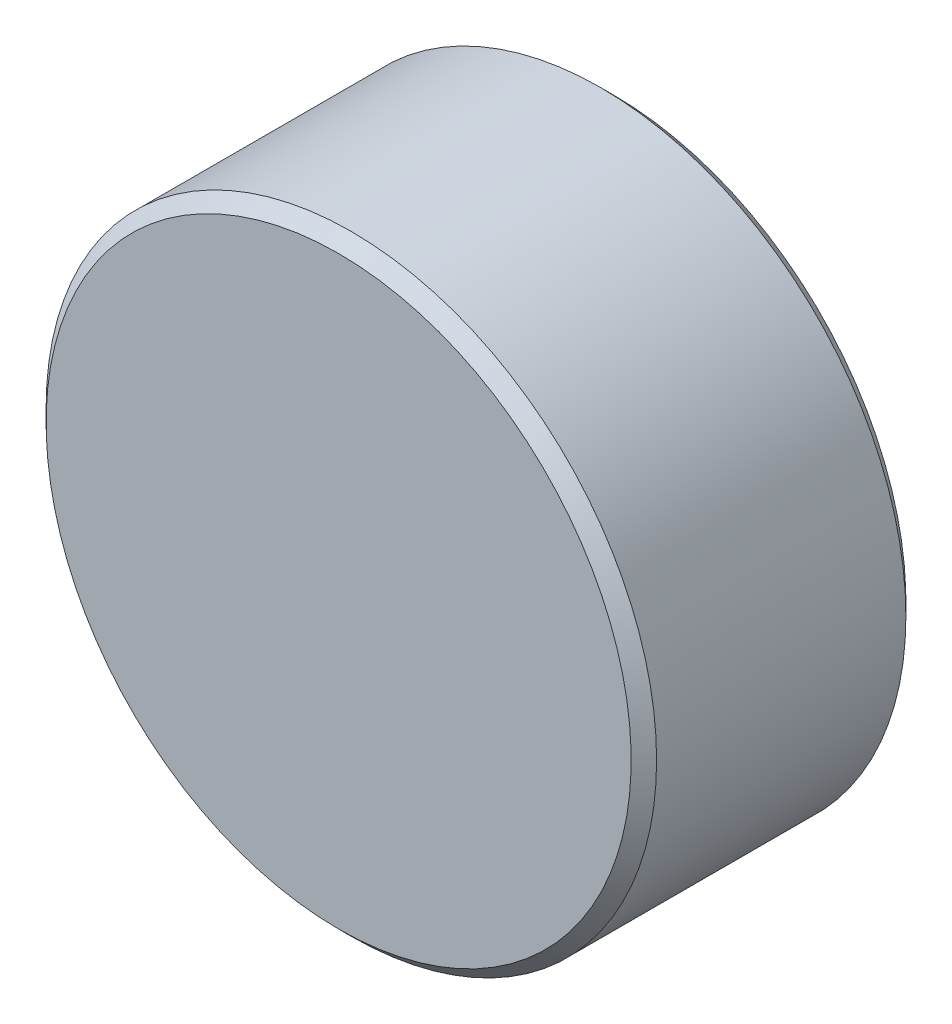
SolidWorks part; units mm, degrees
material "AISI 316 Annealed Stainless Steel Bar (SS)"
ref_plane "Front Plane" through (0, 0, 0) normal (0, 0, 1) x (1, 0, 0)
ref_plane "Top Plane" through (0, 0, 0) normal (0, 1, 0) x (1, 0, 0)
ref_plane "Right Plane" through (0, 0, 0) normal (1, 0, 0) x (0, 0, -1)
sketch "Sketch1" plane through (0, 0, 0) normal (1, 0, 0) x (0, 0, -1)
  line L0 (14.2875, 0) -> (-14.2875, 0) construction
  line L1 (-14.2875, 31.75) -> (-14.2875, -31.75) construction
  line L2 (14.2875, 24.4094) -> (14.2875, -24.4094) construction
  line L3 (14.2875, 24.4094) -> (0.8001, 24.4094) construction
  point P4 (0, 0)
  dimension "OD" = 63.5
  dimension "Length" = 28.575
  dimension "ID" = 48.8188
  dimension "Socket Depth" = 13.4874
sketch "Sketch2" plane through (0, 0, 0) normal (1, 0, 0) x (0, 0, -1)
  line L0 (-14.2875, 0) -> (-14.2875, 30.4271)
  line L1 (-14.2875, 30.4271) -> (-12.9646, 31.75)
  line L2 (-12.9646, 31.75) -> (12.9646, 31.75)
  line L3 (12.9646, 31.75) -> (14.2875, 30.4271)
  line L4 (14.2875, 30.4271) -> (14.2875, 25.7323)
  line L5 (14.2875, 25.7323) -> (12.9646, 24.4094)
  line L6 (14.2875, 24.4094) -> (0.8001, 24.4094) construction
  line L7 (12.9646, 24.4094) -> (0.8001, 24.4094)
  line L8 (0.8001, 24.4094) -> (0.8001, 0)
  line L9 (14.2875, 0) -> (-14.2875, 0) construction
  line L10 (-14.2875, 30.4271) -> (-14.2875, 31.75) construction
  line L11 (-14.2875, 31.75) -> (-12.9646, 31.75) construction
  line L12 (14.2875, 24.4094) -> (14.2875, -24.4094) construction
  line L13 (14.2875, 0) -> (-14.2875, 0) construction
  line L14 (-14.2875, 0) -> (0.8001, 0)
  line L15 (12.9646, -24.4094) -> (0.8001, -24.4094) construction
  line L16 (12.9646, -24.4094) -> (14.2875, -25.7323) construction
  dimension "D1" = 1.3229
revolve "Revolve1" add sketch "Sketch2" angle 360 about L13
sketch "Sketch3" plane through (0, 0, -14.2875) normal (0, 0, -1) x (-1, 0, 0)
  line L0 (0, 0) -> (0, -24.4094) construction
  line L1 (0, 0) -> (-12.2047, -21.1392) construction
  circle A1 centre (0, 0) radius 24.4094 construction
  point P7 (-12.2047, -21.1392)
  dimension "D1" = 30
equation "\"D1@Sketch2\"=\"OD@Sketch1\"/48"
